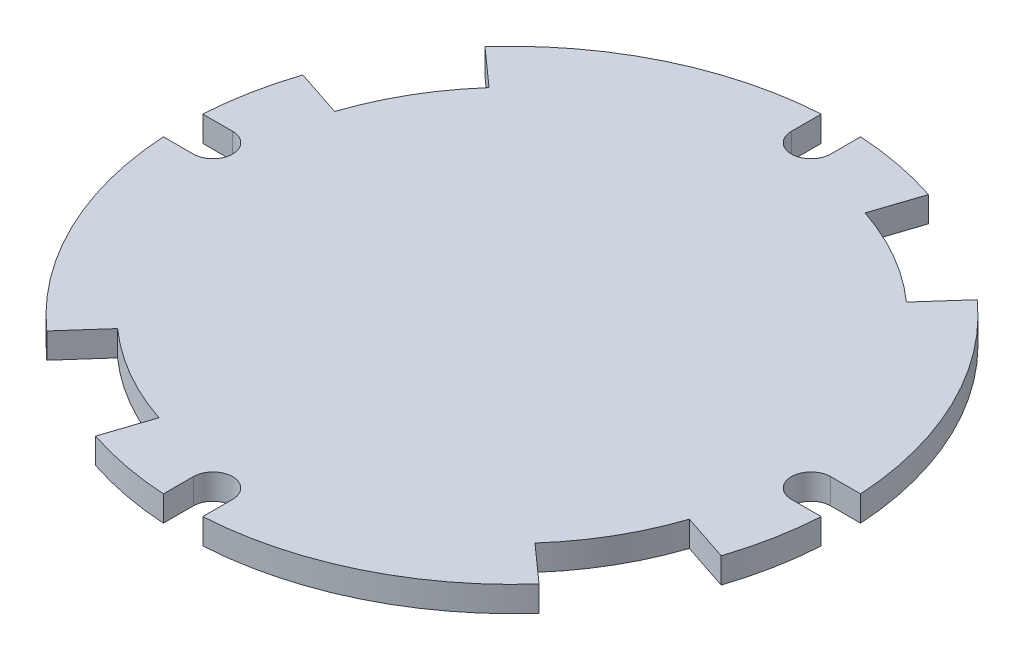
SolidWorks part; units mm, degrees
ref_plane "Plan de face" through (0, 0, 0) normal (0, 0, 1) x (1, 0, 0)
ref_plane "Plan de dessus" through (0, 0, 0) normal (0, 1, 0) x (1, 0, 0)
ref_plane "Plan de droite" through (0, 0, 0) normal (1, 0, 0) x (0, 0, -1)
sketch "Esquisse1" plane through (0, 0, 0) normal (0, 1, 0) x (1, 0, 0)
  circle A0 centre (0, 0) radius 25.95
extrude "Boss.-Extru.1" add sketch "Esquisse1" along normal blind 2
sketch "Esquisse2" plane through (0, 0, 0) normal (0, 1, 0) x (1, 0, 0)
  line L0 (0, 28.4711) -> (0, 25.1) construction
  line L1 (-32.7175, 0) -> (33.1219, 0) construction
  line L2 (-1.55, 25.9037) -> (-1.55, 23.55)
  line L3 (1.55, 25.9037) -> (1.55, 23.55)
  line L4 (0, 22) -> (0, -30.0888) construction
  line L11 (0, 0) -> (28.0458, 48.5767) construction
  line L12 (8.1601, 24.6336) -> (6.918, 20.884)
  line L13 (17.2533, 19.3836) -> (14.6271, 16.4331)
  arc A1 (-1.55, 23.55) -> (1.55, 23.55) centre (0, 23.55) ccw
  circle A2 centre (0, 0) radius 25.95 construction
  arc A3 (-1.55, 25.9037) -> (1.55, 25.9037) centre (0, 0) cw
  arc A4 (8.1601, 24.6336) -> (17.2533, 19.3836) centre (0, 0) cw
  arc A6 (14.6271, 16.4331) -> (6.918, 20.884) centre (0, 0) ccw
  point P34 (0, 0)
  point P51 (0, 0)
  dimension "D1" = 3.1
  dimension "D3" = 30
  dimension "D4" = 5.25
extrude "Enlèv. mat.-Extru.8" cut sketch "Esquisse2" along normal blind 2
pattern_circular "Répétition circulaire1" count 4 over 360 about axis through (0, 0, 0) along (0, 1, 0) of "Enlèv. mat.-Extru.8"
